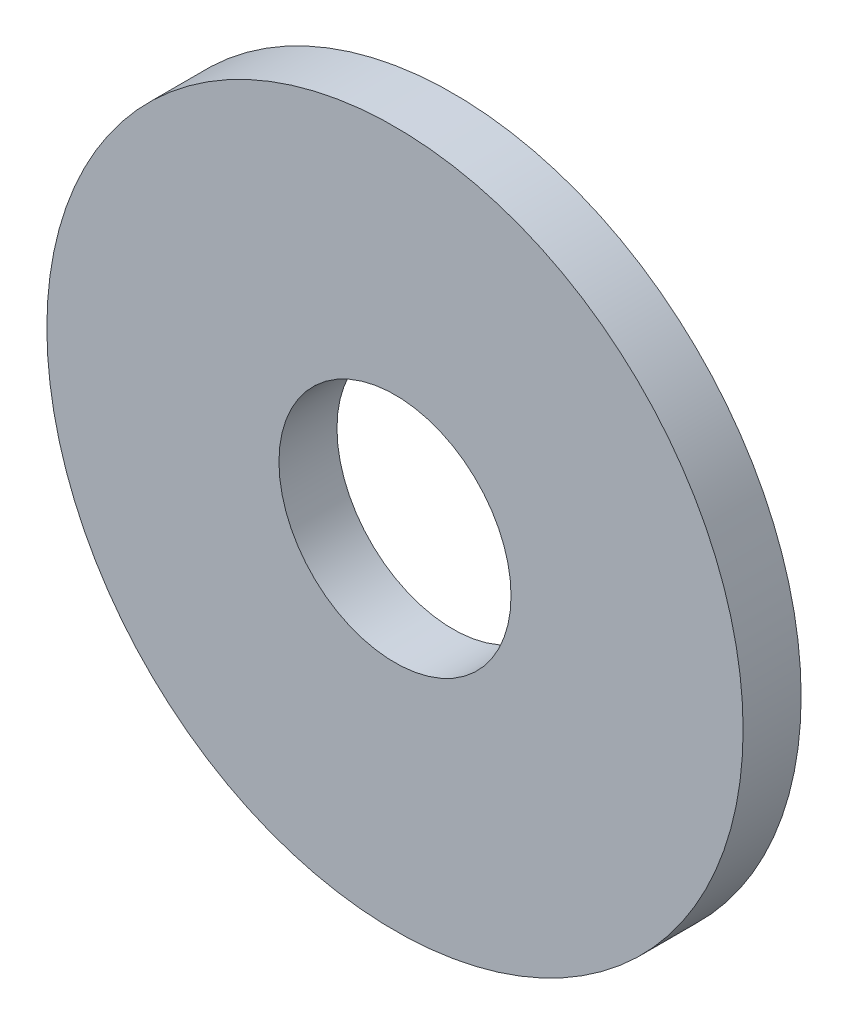
SolidWorks part; units mm, degrees
ref_plane "Plan de face" through (0, 0, 0) normal (0, 0, 1) x (1, 0, 0)
ref_plane "Plan de dessus" through (0, 0, 0) normal (0, 1, 0) x (1, 0, 0)
ref_plane "Plan de droite" through (0, 0, 0) normal (1, 0, 0) x (0, 0, -1)
sketch "Esquisse1" plane through (0, 0, 0) normal (0, 0, 1) x (1, 0, 0)
  circle A0 centre (0, 0) radius 6
  circle A1 centre (0, 0) radius 2
  dimension "D1" = 4
  dimension "D2" = 12
extrude "Boss.-Extru.1" add sketch "Esquisse1" along normal blind 1
